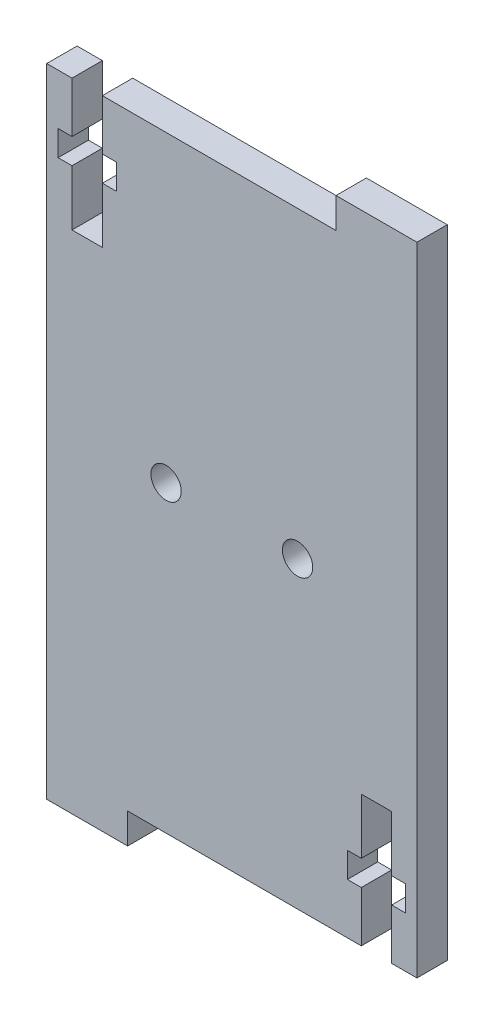
SolidWorks part; units mm, degrees
ref_plane "Plano frontal" through (0, 0, 0) normal (0, 0, 1) x (1, 0, 0)
ref_plane "Plano superior" through (0, 0, 0) normal (0, 1, 0) x (1, 0, 0)
ref_plane "Plano direito" through (0, 0, 0) normal (1, 0, 0) x (0, 0, -1)
sketch "Esboço1" plane through (0, 0, 0) normal (0, 0, 1) x (1, 0, 0)
  line L7 (22.3, -30) -> (22.3, -25)
  line L35 (22.3, -17) -> (19.3, -17)
  line L58 (19.3, -17) -> (19.3, -22.5)
  line L59 (23.675, -22.5) -> (22.3, -22.5)
  line L60 (17.925, -22.5) -> (17.925, -25)
  line L65 (17.925, -25) -> (19.3, -25)
  line L70 (23.675, -25) -> (23.675, -22.5)
  line L91 (22.3, -25) -> (23.675, -25)
  line L92 (22.3, -22.5) -> (22.3, -17)
  line L93 (19.3, -22.5) -> (17.925, -22.5)
  line L94 (19.3, -25) -> (19.3, -30)
  line L95 (-11.8, 30) -> (-11.8, 8.3)
  line L96 (24.8, 33) -> (24.8, -30)
  line L97 (24.8, -30) -> (22.3, -30)
  line L98 (-3.8, -33) -> (-11.8, -33)
  line L99 (-11.8, -33) -> (-11.8, -30)
  line L100 (-3.8, -33) -> (-3.8, -30)
  line L102 (16.8, 30) -> (16.8, 33)
  line L103 (24.8, 33) -> (16.8, 33)
  line L105 (16.8, 30) -> (-6.3, 30)
  line L106 (-4.925, 22.5) -> (-4.925, 25)
  line L107 (-9.3, 30) -> (-9.3, 25)
  line L108 (-9.3, 17) -> (-6.3, 17)
  line L109 (-6.3, 17) -> (-6.3, 22.5)
  line L110 (-10.675, 22.5) -> (-9.3, 22.5)
  line L111 (-4.925, 25) -> (-6.3, 25)
  line L112 (-10.675, 25) -> (-10.675, 22.5)
  line L113 (-9.3, 25) -> (-10.675, 25)
  line L114 (-9.3, 22.5) -> (-9.3, 17)
  line L115 (-6.3, 22.5) -> (-4.925, 22.5)
  line L116 (-6.3, 25) -> (-6.3, 30)
  line L117 (-9.3, 30) -> (-11.8, 30)
  line L118 (19.3, -30) -> (-3.8, -30)
  line L119 (-11.8, -30) -> (-11.8, 8.3)
  circle A4 centre (0, 0) radius 1.5
  circle A6 centre (13, 0) radius 1.5
extrude "Ressalto-extrusão1" add sketch "Esboço1" along normal blind 3
